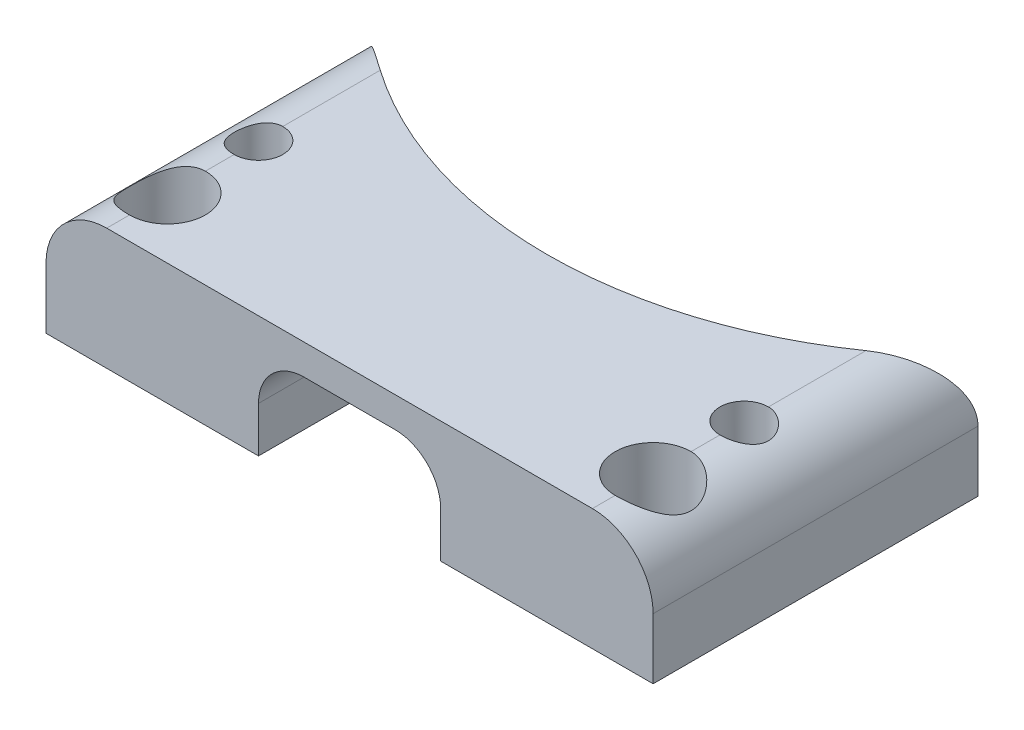
SolidWorks part; units mm, degrees
ref_plane "Front" through (0, 0, 0) normal (0, 0, 1) x (1, 0, 0)
ref_plane "Top" through (0, 0, 0) normal (0, 1, 0) x (1, 0, 0)
ref_plane "Right" through (0, 0, 0) normal (1, 0, 0) x (0, 0, -1)
sketch "Sketch5" plane through (0, 0, 0) normal (0, 1, 0) x (1, 0, 0)
  line L0 (0, 0) -> (0, 14) construction
  line L1 (-10, -6.5) -> (10, -6.5)
  line L2 (-10, -6.5) -> (-10, 4.202)
  line L6 (10, -6.5) -> (10, 4.202)
  arc A0 (-10, 4.202) -> (10, 4.202) centre (0, 14) ccw
extrude "Boss-Extrude1" add sketch "Sketch5" against normal blind 4
sketch "Sketch3" plane through (0, 0, 0) normal (0, 0, 1) x (1, 0, 0)
  line L0 (0, -4) -> (0, -2.5) construction
  line L1 (0, -4) -> (-3, -4)
  line L3 (0, -2.5) -> (1.5, -2.5) construction
  line L4 (0, -2.5) -> (-1.5, -2.5) construction
  line L5 (-3, -4) -> (-3, -2.5)
  line L6 (0, -4) -> (3, -4)
  line L7 (3, -4) -> (3, -2.5)
  line L8 (-1.5, -1) -> (1.5, -1)
  arc A0 (-3, -2.5) -> (-1.5, -1) centre (-1.5, -2.5) cw
  arc A1 (3, -2.5) -> (1.5, -1) centre (1.5, -2.5) ccw
extrude "Cut-Extrude1" cut sketch "Sketch3" against normal through all from offset 6.5 contours L7 A1 L8 A0 L5 L1 L6
fillet "Fillet1" radius 2 2 edges at (10, 0, 1.149) (-10, 0, 1.149)
sketch "Sketch2" plane through (0, 0, 0) normal (0, 1, 0) x (1, 0, 0)
  line L0 (0, 0) -> (0, -1.5) construction
  line L2 (0, -1.5) -> (-8, -1.5) construction
  line L3 (0, -1.5) -> (8, -1.5) construction
  line L5 (0, -1.5) -> (0, -4.5) construction
  line L6 (0, -4.5) -> (-8, -4.5) construction
  line L7 (0, -4.5) -> (8, -4.5) construction
  circle A0 centre (-8, -1.5) radius 0.8
  circle A1 centre (8, -1.5) radius 0.8
  circle A2 centre (8, -4.5) radius 0.8
  circle A3 centre (-8, -4.5) radius 0.8
extrude "Screw Holes" cut sketch "Sketch2" against normal through all
sketch "Sketch4" plane through (0, 0, 0) normal (0, 1, 0) x (1, 0, 0)
  circle A0 centre (-8, -4.5) radius 1.25
  circle A1 centre (8, -4.5) radius 1.25
extrude "Screw Heads" cut sketch "Sketch4" against normal blind 3
